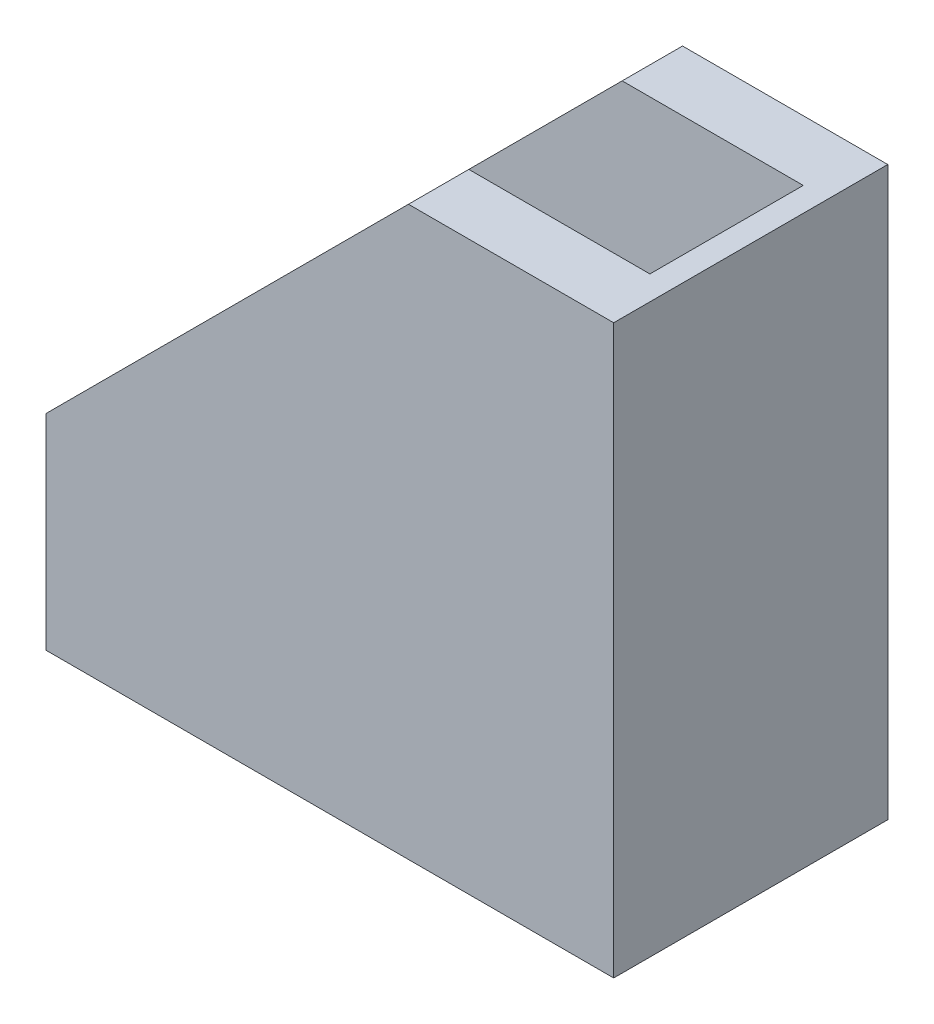
SolidWorks part; units mm, degrees
ref_plane "Front" through (0, 0, 0) normal (0, 0, 1) x (1, 0, 0)
ref_plane "Top" through (0, 0, 0) normal (0, 1, 0) x (1, 0, 0)
ref_plane "Right" through (0, 0, 0) normal (1, 0, 0) x (0, 0, -1)
other "Configuration Table"
sketch "Sketch1" plane through (0, 0, 0) normal (0, 0, 1) x (1, 0, 0)
  line L0 (0, 0) -> (0, 47)
  line L1 (0, 47) -> (-17, 47)
  line L2 (0, 0) -> (-47, 0)
  line L3 (-47, 0) -> (-47, 17)
  line L4 (-17, 47) -> (-47, 17)
extrude "Boss-Extrude1" add sketch "Sketch1" along normal mid plane 22.7
sketch "Sketch2" plane through (0, 0, 0) normal (0, 0, 1) x (1, 0, 0)
  line L0 (-47, 17) -> (-47, 2)
  line L1 (-47, 17) -> (-47, 0) construction
  line L2 (-17, 47) -> (-2, 47)
  line L3 (0, 47) -> (-17, 47) construction
  line L4 (-2, 47) -> (-2, 2)
  line L5 (-2, 2) -> (-47, 2)
  line L6 (-47, 17) -> (-17, 47)
extrude "Cut-Extrude1" cut sketch "Sketch2" against normal mid plane 12.7
